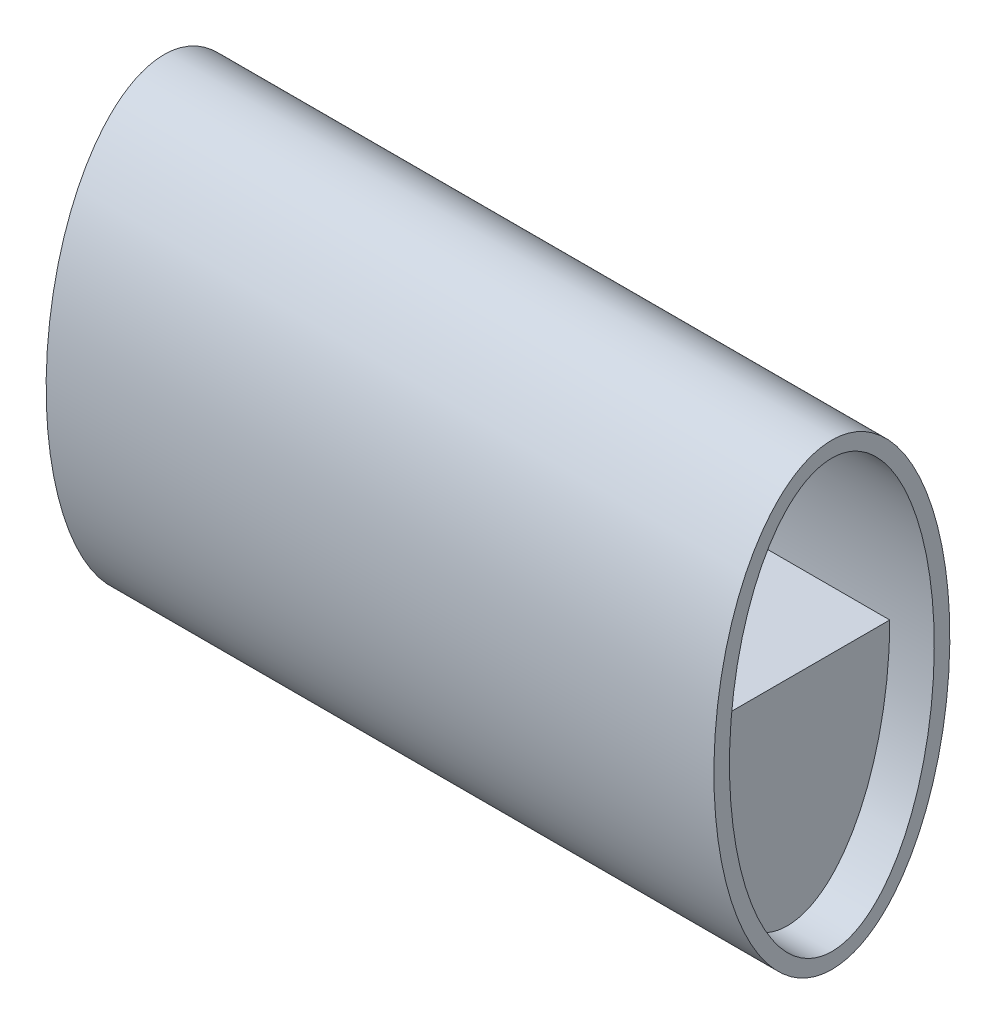
SolidWorks part; units mm, degrees
ref_plane "Спереди" through (0, 0, 0) normal (0, 0, 1) x (1, 0, 0)
ref_plane "Сверху" through (0, 0, 0) normal (0, 1, 0) x (1, 0, 0)
ref_plane "Справа" through (0, 0, 0) normal (1, 0, 0) x (0, 0, -1)
sketch "Эскиз1" plane through (0, 0, 0) normal (1, 0, 0) x (0, 0, -1)
  ellipse E0 centre (0, 0) end of major axis (0, -103) minor radius 53
  ellipse E1 centre (0, 0) end of major axis (0, -96) minor radius 46
  dimension "D1" = 106
  dimension "D2" = 7
  dimension "D3" = 7
  dimension "D4" = 206
  dimension "D6" = 92
extrude "Бобышка-Вытянуть1" add sketch "Эскиз1" along normal blind 300
ref_plane "Плоскость1" through (150, 0, 0) normal (-1, 0, 0) x (0, 0, 1)
sketch "Эскиз2" plane through (150, 0, 0) normal (-1, 0, 0) x (0, 0, 1)
  ellipse E0 centre (0, 0) end of major axis (0, -96) minor radius 46 construction
  ellipse E1 centre (0, 0) end of major axis (0, -96) minor radius 46
  dimension "D1" = 192
  dimension "D2" = 92
extrude "Бобышка-Вытянуть2" add sketch "Эскиз2" along normal blind 30 and the other way blind 30
sketch "Эскиз3" plane through (150, 0, 0) normal (-1, 0, 0) x (0, 0, 1)
  ellipse E0 centre (0, 0) end of major axis (0, 96) minor radius 46
  ellipse E1 centre (0, 0) end of major axis (0, -96) minor radius 46 construction
  ellipse E2 centre (0, 0) end of major axis (0, -96) minor radius 46 construction
extrude "Вырез-Вытянуть1" cut sketch "Эскиз3" against normal blind 27 and the other way blind 27
sketch "Эскиз4" plane through (120, 0, 0) normal (-1, 0, 0) x (0, 0, 1)
  line L0 (-46, 0) -> (46, 0)
  ellipse E0 centre (0, 0) end of major axis (0, -96) minor radius 46 (-46, 0) -> (46, 0) ccw
  ellipse E1 centre (0, 0) end of major axis (0, -96) minor radius 46 construction
extrude "Бобышка-Вытянуть3" add sketch "Эскиз4" along normal offset from surface (100 mm away) 20 up to face at (0, -103, 0)
sketch "Эскиз5" plane through (180, 0, 0) normal (1, 0, 0) x (0, 0, -1)
  line L0 (-46, 0) -> (46, 0)
  ellipse E0 centre (0, 0) end of major axis (0, -96) minor radius 46 (-46, 0) -> (46, 0) ccw
  ellipse E1 centre (0, 0) end of major axis (0, -96) minor radius 46 construction
  ellipse E2 centre (0, 0) end of major axis (0, -96) minor radius 46 construction
extrude "Бобышка-Вытянуть4" add sketch "Эскиз5" along normal offset from surface (100 mm away) 20 up to face at (300, -103, 0)
sketch "Эскиз6" plane through (123, 0, 0) normal (1, 0, 0) x (0, 0, -1)
  line L0 (46, 0) -> (-46, 0) construction
  line L1 (-46, 0) -> (46, 0)
  ellipse E0 centre (0, 0) end of major axis (0, -96) minor radius 46 (-46, 0) -> (46, 0) ccw
  ellipse E1 centre (0, 0) end of major axis (0, -96) minor radius 46 (-46, 0) -> (46, 0) ccw construction
  ellipse E2 centre (0, 0) end of major axis (0, -96) minor radius 46 construction
extrude "Бобышка-Вытянуть5" add sketch "Эскиз6" along normal up to surface (54 mm away) up to face at (177, 96, 0)
